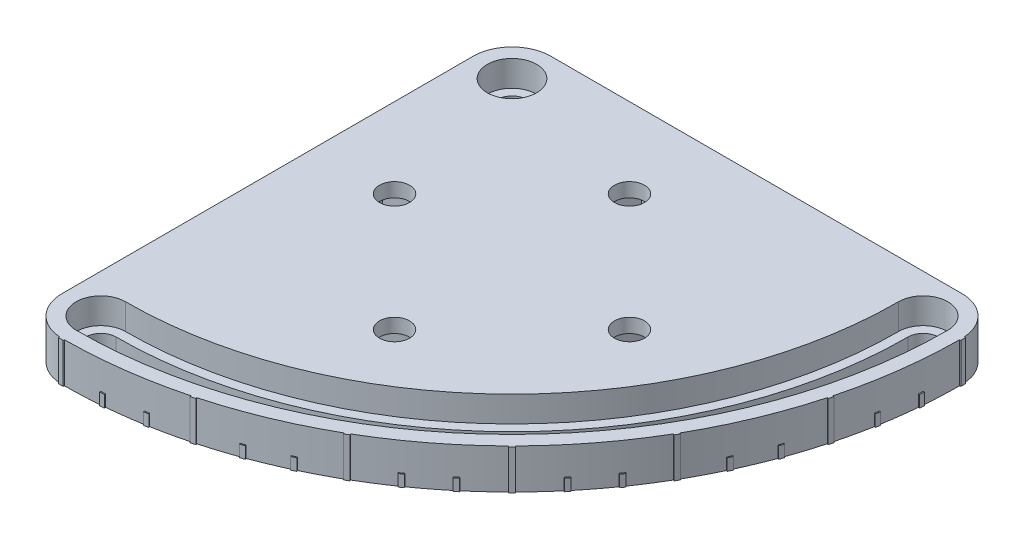
SolidWorks part; units mm, degrees
ref_plane "정면" through (0, 0, 0) normal (0, 0, 1) x (1, 0, 0)
ref_plane "윗면" through (0, 0, 0) normal (0, 1, 0) x (1, 0, 0)
ref_plane "우측면" through (0, 0, 0) normal (1, 0, 0) x (0, 0, -1)
sketch "스케치1" plane through (0, 0, 0) normal (0, 1, 0) x (1, 0, 0)
  line L1 (-8.25, -87.5) -> (-8.25, -22.5)
  line L7 (22.5, 8.25) -> (87.5, 8.25)
  arc A0 (0, -19.25) -> (0, -25.75) centre (0, -22.5) ccw
  arc A1 (25.75, 0) -> (19.25, 0) centre (22.5, 0) ccw
  arc A2 (0, -84.25) -> (0, -90.75) centre (0, -87.5) ccw
  arc A3 (90.75, 0) -> (84.25, 0) centre (87.5, 0) ccw
  arc A4 (0, -25.75) -> (25.75, 0) centre (0, 0) ccw
  arc A5 (0, -19.25) -> (19.25, 0) centre (0, 0) ccw
  arc A6 (0, -84.25) -> (84.25, 0) centre (0, 0) ccw
  arc A7 (0, -90.75) -> (90.75, 0) centre (0, 0) ccw
  circle A8 centre (58.75, -33.75) radius 3.2
  circle A9 centre (33.75, -58.75) radius 3.2
  circle A10 centre (8.75, -33.75) radius 3.2
  circle A11 centre (33.75, -8.75) radius 3.2
  arc A12 (0, -95.75) -> (95.75, 0) centre (0, 0) ccw
  arc A13 (0, -14.25) -> (14.25, 0) centre (0, 0) ccw
  arc A15 (-8.25, -87.5) -> (0, -95.75) centre (0, -87.5) ccw
  arc A16 (95.75, 0) -> (87.5, 8.25) centre (87.5, 0) ccw
  arc A17 (0, -14.25) -> (-8.25, -22.5) centre (0, -22.5) ccw
  arc A18 (22.5, 8.25) -> (14.25, 0) centre (22.5, 0) ccw
  point P0 (33.75, -33.75)
  dimension "D7" = 25
  dimension "D10" = 6.4
  dimension "D3" = 6.5
  dimension "D6" = 25
  dimension "D14" = 5
  dimension "D1" = 33.75
  dimension "D2" = 33.75
  dimension "D4" = 22.5
  dimension "D5" = 87.5
  dimension "D8" = 25
  dimension "D9" = 25
extrude "보스-돌출1" add sketch "스케치1" along normal blind 8.5
sketch "스케치2" plane through (0, 8.5, 0) normal (0, 1, 0) x (1, 0, 0)
  line L0 (0, 0) -> (-0.5027, -95.9987) construction
  line L1 (0, 0) -> (0.5027, -95.9987) construction
  line L2 (0, 0) -> (0, -96) construction
  line L3 (0.4974, -94.9987) -> (0.5027, -95.9987)
  line L4 (-0.4974, -94.9987) -> (-0.5027, -95.9987)
  arc A0 (-0.5027, -95.9987) -> (0.5027, -95.9987) centre (0, 0) ccw
  arc A1 (-0.4974, -94.9987) -> (0.4974, -94.9987) centre (0, 0) ccw
  dimension "D3" = 190
  dimension "D4" = 96
  dimension "D1" = 0.3
  dimension "D2" = 0.3
extrude "보스-돌출2" add sketch "스케치2" against normal up to surface (8.5 mm away) up to face at (12.7675, 0, 12.7675)
pattern_circular "원형 패턴1" count 7 over 90 about axis through (0, 0, 0) along (0, 1, 0) of "보스-돌출2"
sketch "스케치6" plane through (0, 0, 0) normal (0, -1, 0) x (1, 0, 0)
  line L2 (0, 0) -> (95.75, 0) construction
  line L3 (0, 0) -> (95.7487, 0.5013) construction
  line L6 (0, 0) -> (95.7348, -0.5013) construction
  line L7 (95.9987, 0.5027) -> (95.4987, 0.5)
  line L8 (95.9987, -0.5027) -> (95.4987, -0.5)
  arc A1 (95.4987, -0.5) -> (95.4987, 0.5) centre (0, 0) ccw
  arc A2 (95.9987, -0.5027) -> (95.9987, 0.5027) centre (0, 0) ccw
  arc A4 (95.7487, 0.5013) -> (92.6159, 24.2973) centre (0, 0) ccw construction
  arc A5 (87.5, -8.25) -> (95.7348, -0.5013) centre (87.5, 0) ccw construction
  dimension "D1" = 191
  dimension "D2" = 0.3
  dimension "D4" = 96
  dimension "D3" = 0.3
extrude "보스-돌출3" add sketch "스케치6" against normal blind 2.5
pattern_circular "원형 패턴2" count 19 over 90 about axis through (0, 8.5, 0) along (0, -1, 0) of "보스-돌출3"
sketch "스케치7" plane through (0, 0, 0) normal (0, -1, 0) x (1, 0, 0)
  line L0 (0, 0) -> (8.75, 33.75) construction
  line L1 (0, 0) -> (33.75, 58.75) construction
  line L2 (58.75, 33.75) -> (0, 0) construction
  line L3 (0, 0) -> (33.75, 8.75) construction
  line L4 (26.6508, 56.8313) -> (35.6687, 51.6508)
  line L5 (26.6508, 56.8313) -> (31.8313, 65.8492)
  line L6 (35.6687, 51.6508) -> (40.8492, 60.6687)
  line L7 (31.8313, 65.8492) -> (40.8492, 60.6687)
  line L8 (26.6508, 56.8313) -> (40.8492, 60.6687) construction
  line L9 (35.6687, 51.6508) -> (31.8313, 65.8492) construction
  line L10 (51.6508, 35.6687) -> (56.8313, 26.6508)
  line L11 (51.6508, 35.6687) -> (60.6687, 40.8492)
  line L12 (56.8313, 26.6508) -> (65.8492, 31.8313)
  line L13 (60.6687, 40.8492) -> (65.8492, 31.8313)
  line L14 (51.6508, 35.6687) -> (65.8492, 31.8313) construction
  line L15 (56.8313, 26.6508) -> (60.6687, 40.8492) construction
  line L16 (30.0214, 2.4114) -> (40.0886, 5.0214)
  line L17 (30.0214, 2.4114) -> (27.4114, 12.4786)
  line L18 (40.0886, 5.0214) -> (37.4786, 15.0886)
  line L19 (27.4114, 12.4786) -> (37.4786, 15.0886)
  line L20 (30.0214, 2.4114) -> (37.4786, 15.0886) construction
  line L21 (40.0886, 5.0214) -> (27.4114, 12.4786) construction
  line L22 (2.4114, 30.0214) -> (12.4786, 27.4114)
  line L23 (2.4114, 30.0214) -> (5.0214, 40.0886)
  line L24 (12.4786, 27.4114) -> (15.0886, 37.4786)
  line L25 (5.0214, 40.0886) -> (15.0886, 37.4786)
  line L26 (2.4114, 30.0214) -> (15.0886, 37.4786) construction
  line L27 (12.4786, 27.4114) -> (5.0214, 40.0886) construction
  point P5 (33.75, 58.75)
  point P6 (58.75, 33.75)
  point P7 (33.75, 8.75)
  point P12 (8.75, 33.75)
  dimension "D1" = 10.4
extrude "컷-돌출1" cut sketch "스케치7" against normal offset from surface (5.5 mm away) 3 up to face at (51.7143, 8.5, 51.7143)
sketch "스케치8" plane through (0, 8.5, 0) normal (0, 1, 0) x (1, 0, 0)
  arc A0 (27.75, 0) -> (17.25, 0) centre (22.5, 0) ccw
  arc A1 (92.75, 0) -> (82.25, 0) centre (87.5, 0) ccw
  arc A2 (0, -17.25) -> (0, -27.75) centre (0, -22.5) ccw
  arc A3 (0, -82.25) -> (0, -92.75) centre (0, -87.5) ccw
  arc A4 (0, -17.25) -> (17.25, 0) centre (0, 0) ccw
  arc A5 (0, -27.75) -> (27.75, 0) centre (0, 0) ccw
  arc A6 (0, -82.25) -> (82.25, 0) centre (0, 0) ccw
  arc A7 (0, -92.75) -> (92.75, 0) centre (0, 0) ccw
  dimension "D1" = 10.5
extrude "컷-돌출2" cut sketch "스케치8" against normal offset from surface (5.5 mm away) 3 up to face at (58.75, 0, 33.75)
sketch "스케치9" plane through (0, 8.5, 0) normal (0, 1, 0) x (1, 0, 0)
  line L0 (-8.25, -22.5) -> (-8.25, 0)
  line L1 (22.5, 8.25) -> (0, 8.25)
  line L2 (-8.25, -22.5) -> (-8.25, -27.75)
  line L3 (27.75, 8.25) -> (22.5, 8.25)
  line L4 (87.5, 8.25) -> (22.5, 8.25) construction
  line L5 (0, -27.75) -> (-8.25, -27.75)
  line L6 (-8.25, -22.5) -> (-8.25, -87.5) construction
  line L7 (27.75, 0) -> (27.75, 8.25)
  arc A0 (0, -27.75) -> (27.75, 0) centre (0, 0) ccw
  arc A1 (0, 8.25) -> (-8.25, 0) centre (0, 0) ccw
  arc A2 (0, -27.75) -> (27.75, 0) centre (0, 0) ccw construction
extrude "보스-돌출4" add sketch "스케치9" against normal up to surface (8.5 mm away) up to face at (58.75, 0, 33.75)
sketch "스케치10" plane through (0, 8.5, 0) normal (0, 1, 0) x (1, 0, 0)
  circle A0 centre (0, 0) radius 3.25
  arc A2 (0, -84.25) -> (0, -90.75) centre (0, -87.5) ccw construction
extrude "컷-돌출3" cut sketch "스케치10" against normal up to surface (8.5 mm away) up to face at (58.75, 0, 33.75)
sketch "스케치11" plane through (0, 8.5, 0) normal (0, 1, 0) x (1, 0, 0)
  circle A0 centre (0, 0) radius 5.25
  arc A1 (0, -82.25) -> (0, -92.75) centre (0, -87.5) ccw construction
extrude "컷-돌출4" cut sketch "스케치11" against normal offset from surface (5.5 mm away) 3 up to face at (0, 0, 3.25)
